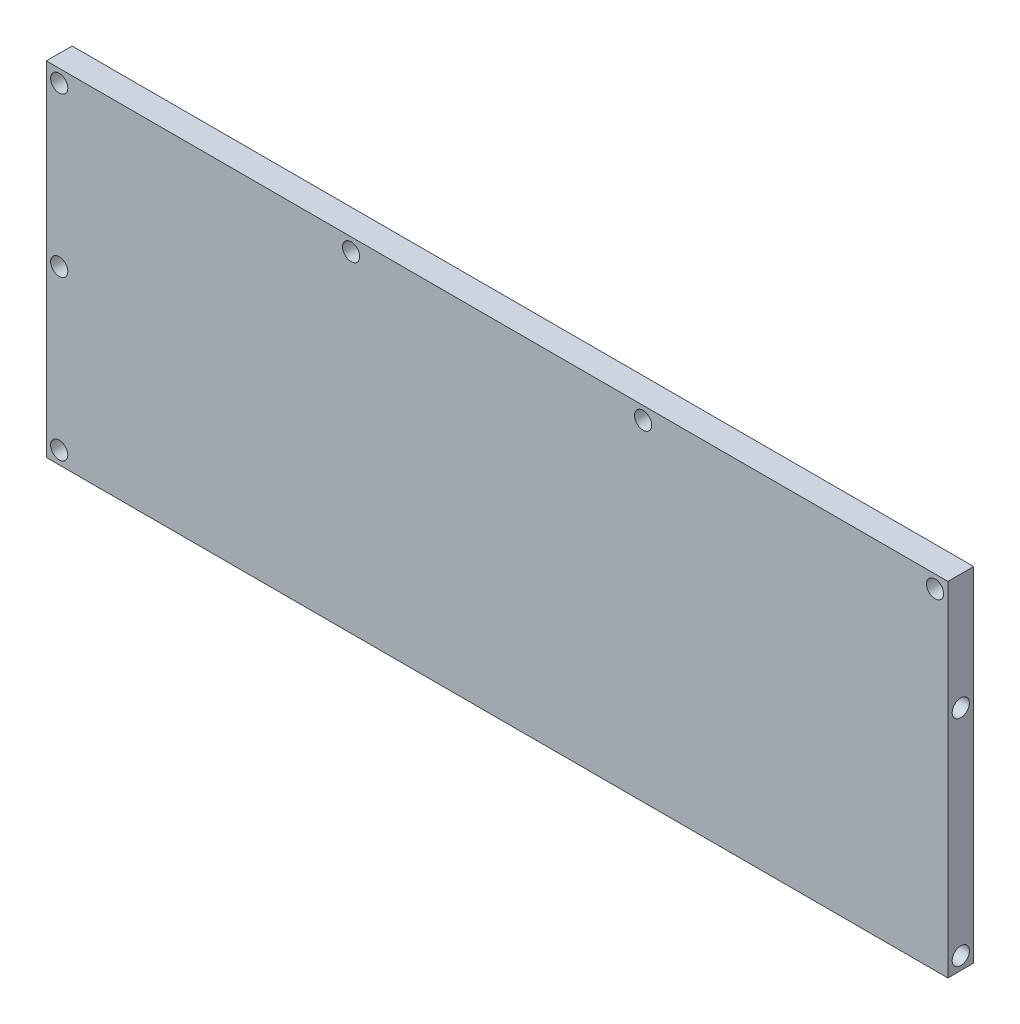
SolidWorks part; units mm, degrees
material "6061 合金"
ref_plane "前视" through (0, 0, 0) normal (0, 0, 1) x (1, 0, 0)
ref_plane "上视" through (0, 0, 0) normal (0, 1, 0) x (1, 0, 0)
ref_plane "右视" through (0, 0, 0) normal (1, 0, 0) x (0, 0, -1)
sketch "草图1" plane through (0, 0, 0) normal (0, 0, 1) x (1, 0, 0)
  line L0 (-105, -40) -> (105, -40)
  line L1 (-105, -40) -> (-105, 40)
  line L2 (105, -40) -> (105, 40)
  line L3 (-105, 40) -> (105, 40)
  line L4 (-105, -40) -> (105, 40) construction
  line L5 (105, -40) -> (-105, 40) construction
  point P1 (0, 0)
  dimension "D1" = 80
  dimension "D2" = 210
extrude "凸台-拉伸1" add sketch "草图1" along normal blind 6
sketch "草图2" plane through (0, 0, 6) normal (0, 0, 1) x (1, 0, 0)
  line L0 (-105, 40) -> (-105, -40) construction
  line L1 (105, 40) -> (-105, 40) construction
  circle A0 centre (-102, 0) radius 2
  circle A1 centre (-102, 37) radius 2
  circle A2 centre (-102, -37) radius 2
  circle A3 centre (-34, 37) radius 2
  circle A4 centre (34, 37) radius 2
  circle A5 centre (102, 37) radius 2
  dimension "D1" = 3
  dimension "D2" = 3
  dimension "D3" = 3
  dimension "D5" = 37
  dimension "D6" = 37
  dimension "D4" = 4
extrude "切除-拉伸1" cut sketch "草图2" against normal blind 6
sketch "草图3" plane through (105, 0, 0) normal (1, 0, 0) x (0, 0, -1)
  line L0 (-6, -40) -> (0, -40) construction
  circle A0 centre (-3, -37) radius 2
  circle A1 centre (-3, 13) radius 2
  dimension "D1" = 3
  dimension "D2" = 2
extrude "切除-拉伸2" cut sketch "草图3" against normal blind 20
